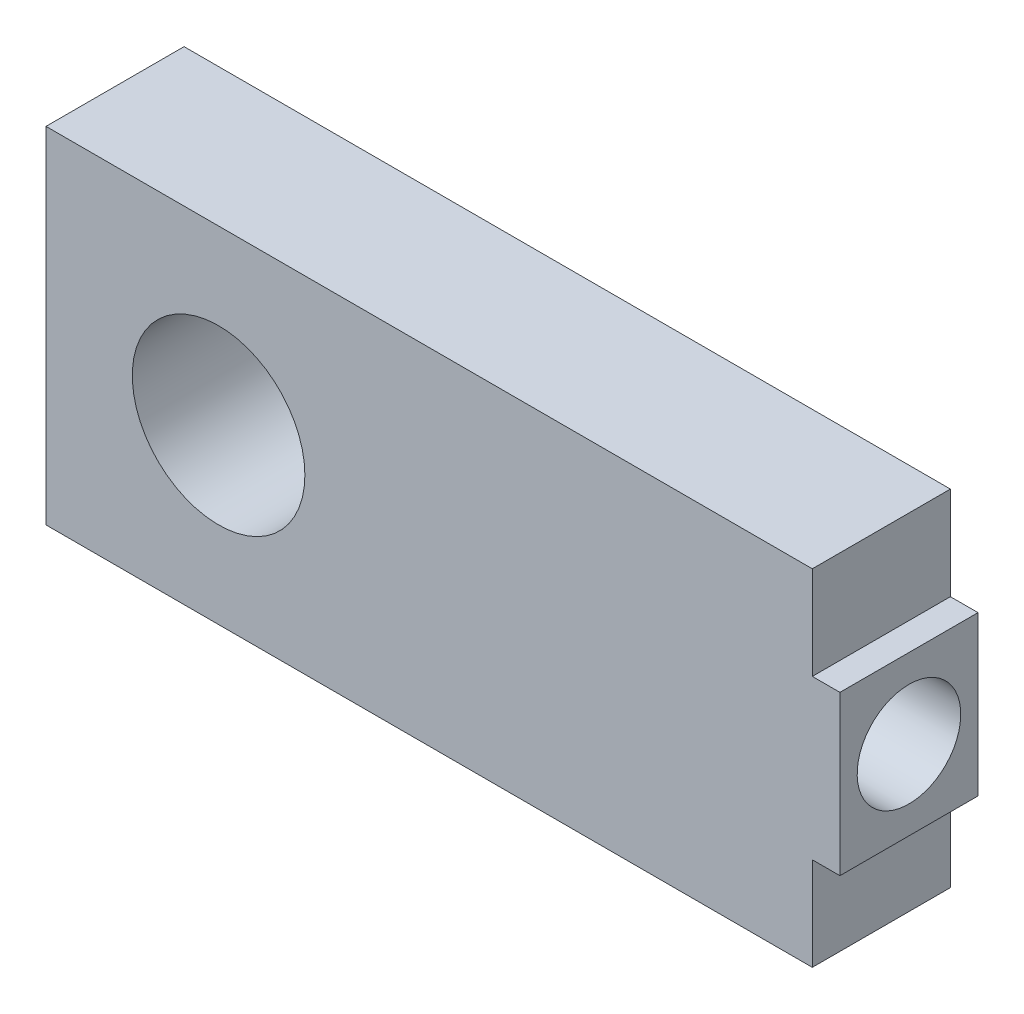
SolidWorks part; units mm, degrees
ref_plane "Front Plane" through (0, 0, 0) normal (0, 0, 1) x (1, 0, 0)
ref_plane "Top Plane" through (0, 0, 0) normal (0, 1, 0) x (1, 0, 0)
ref_plane "Right Plane" through (0, 0, 0) normal (1, 0, 0) x (0, 0, -1)
sketch "Sketch1" plane through (0, 0, 0) normal (0, 0, 1) x (1, 0, 0)
  line L0 (2819.4, -584.2) -> (2819.4, -1270)
  line L1 (2819.4, 1270) -> (-2819.4, 1270)
  line L2 (2819.4, 1270) -> (2819.4, 584.2)
  line L3 (2819.4, -1270) -> (-2819.4, -1270)
  line L4 (-2819.4, 1270) -> (-2819.4, -1270)
  line L5 (2819.4, 1270) -> (-2819.4, -1270) construction
  line L6 (2819.4, -1270) -> (-2819.4, 1270) construction
  line L7 (2819.4, 584.2) -> (3022.6, 584.2)
  line L9 (2819.4, -584.2) -> (3022.6, -584.2)
  line L10 (3022.6, 584.2) -> (3022.6, -584.2)
  circle A0 centre (-1549.4, 0) radius 635
  point P0 (0, 0)
  point P10 (3022.6, 0)
  point P13 (0, 0)
  dimension "D5" = 1270
  dimension "D1" = 2540
  dimension "D2" = 5638.8
  dimension "D3" = 203.2
  dimension "D4" = 1168.4
  dimension "D6" = 1270
extrude "Boss-Extrude1" add sketch "Sketch1" along normal mid plane 1016
sketch "Sketch2" plane through (3022.6, 0, 0) normal (1, 0, 0) x (0, 0, -1)
  circle A0 centre (0, 0) radius 381
  dimension "D1" = 762
extrude "Cut-Extrude1" cut sketch "Sketch2" against normal blind 2540
equation "\"ll\"=2.38552"
